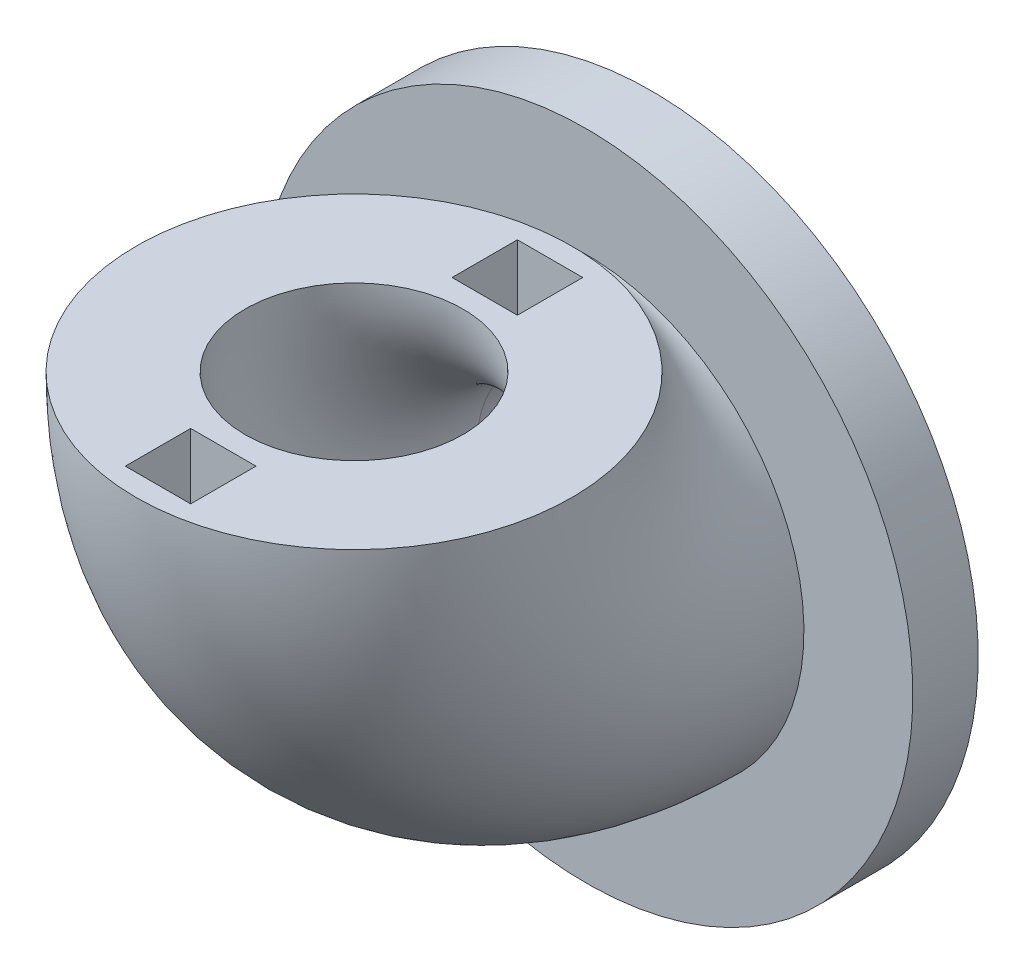
SolidWorks part; units mm, degrees
ref_plane "Front Plane" through (0, 0, 0) normal (0, 0, 1) x (1, 0, 0)
ref_plane "Top Plane" through (0, 0, 0) normal (0, 1, 0) x (1, 0, 0)
ref_plane "Right Plane" through (0, 0, 0) normal (1, 0, 0) x (0, 0, -1)
sketch "Sketch1" plane through (0, 0, 0) normal (0, 0, 1) x (1, 0, 0)
  circle A0 centre (0, 0) radius 5
  circle A1 centre (0, 0) radius 10
sketch "Sketch3" plane through (0, 0, 0) normal (1, 0, 0) x (0, 0, -1)
  line L0 (0, 0) -> (0, 10.6544) construction
  arc A0 (0, 0) -> (-10.6544, 10.6544) centre (0, 10.6544) cw
sweep "Sweep1" add profiles "Sketch1" path "Sketch3"
sketch "Sketch4" plane through (0, 0, 0) normal (0, 0, -1) x (-1, 0, 0)
  circle A0 centre (0, 0) radius 5
  circle A1 centre (0, 0) radius 15
extrude "Boss-Extrude1" add sketch "Sketch4" along normal blind 3
sketch "Sketch5" plane through (0, 10.6544, 0) normal (0, 1, 0) x (1, 0, 0)
  line L0 (0, -5.6544) -> (0, -0.6544) construction
  line L1 (-10, -10.6544) -> (10, -10.6544) construction
  line L2 (-1.5, -1.6544) -> (1.5, -1.6544)
  line L3 (-1.5, -1.6544) -> (-1.5, -4.6544)
  line L4 (-1.5, -4.6544) -> (1.5, -4.6544)
  line L5 (1.5, -1.6544) -> (1.5, -4.6544)
  line L6 (-1.5, -1.6544) -> (1.5, -4.6544) construction
  line L7 (-1.5, -4.6544) -> (1.5, -1.6544) construction
  line L8 (-1.5, -19.6544) -> (1.5, -19.6544)
  line L9 (-1.5, -19.6544) -> (-1.5, -16.6544)
  line L10 (-1.5, -16.6544) -> (1.5, -16.6544)
  line L11 (1.5, -19.6544) -> (1.5, -16.6544)
  circle A0 centre (0, -10.6544) radius 10 construction
  circle A1 centre (0, -10.6544) radius 5 construction
  point P10 (0, -3.1544)
  dimension "D1" = 3
  dimension "D2" = 3
extrude "Cut-Extrude1" cut sketch "Sketch5" against normal blind 3
